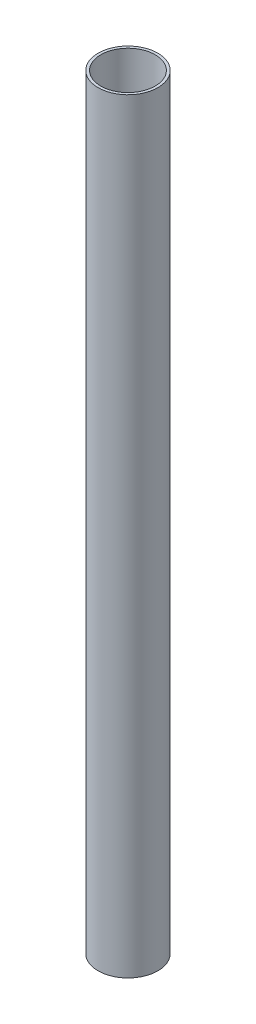
SolidWorks part; units mm, degrees
ref_plane "Front Plane" through (0, 0, 0) normal (0, 0, 1) x (1, 0, 0)
ref_plane "Top Plane" through (0, 0, 0) normal (0, 1, 0) x (1, 0, 0)
ref_plane "Right Plane" through (0, 0, 0) normal (1, 0, 0) x (0, 0, -1)
sketch "Sketch1" plane through (0, 0, 0) normal (0, 1, 0) x (1, 0, 0)
  circle A0 centre (0, 0) radius 7.9375
  circle A1 centre (0, 0) radius 7.2263
  dimension "D1" = 15.875
  dimension "D2" = 14.4526
extrude "Boss-Extrude1" add sketch "Sketch1" along normal blind 203.2
